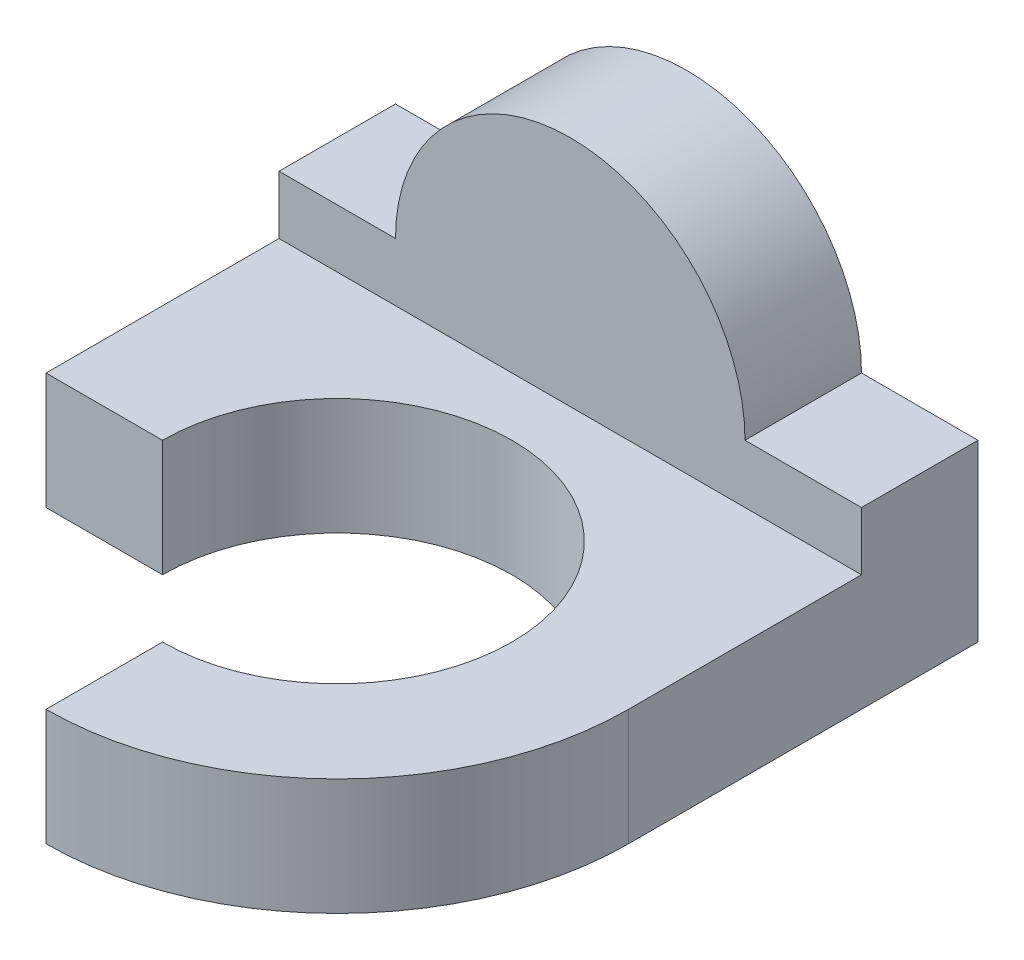
SolidWorks part; units mm, degrees
ref_plane "Front Plane" through (0, 0, 0) normal (0, 0, 1) x (1, 0, 0)
ref_plane "Top Plane" through (0, 0, 0) normal (0, 1, 0) x (1, 0, 0)
ref_plane "Right Plane" through (0, 0, 0) normal (1, 0, 0) x (0, 0, -1)
sketch "Sketch1" plane through (0, 0, 0) normal (0, 0, 1) x (1, 0, 0)
  line L1 (0, 0) -> (100, 0)
  line L2 (0, 0) -> (0, 30)
  line L3 (0, 30) -> (100, 30)
  line L4 (100, 0) -> (100, 30)
  dimension "D1" = 30
  dimension "D2" = 100
extrude "Boss-Extrude1" add sketch "Sketch1" along normal blind 110
sketch "Sketch2" plane through (0, 0, 0) normal (-1, 0, 0) x (0, 0, 1)
  line L1 (110, 30) -> (20, 30)
  line L2 (110, 30) -> (110, 20)
  line L3 (110, 20) -> (20, 20)
  line L4 (20, 30) -> (20, 20)
  dimension "D1" = 10
  dimension "D2" = 20
extrude "Cut-Extrude1" cut sketch "Sketch2" against normal blind 110
sketch "Sketch3" plane through (0, 0, 20) normal (0, 0, 1) x (1, 0, 0)
  line L0 (100, 30) -> (0, 30) construction
  line L1 (20, 30) -> (80, 30)
  arc A0 (20, 30) -> (80, 30) centre (50, 30) cw
  dimension "D1" = 30
extrude "Boss-Extrude2" add sketch "Sketch3" against normal blind 20
sketch "Sketch4" plane through (0, 20, 0) normal (0, 1, 0) x (1, 0, 0)
  line L0 (100, -20) -> (100, -110) construction
  line L3 (50, -110) -> (100, -110)
  line L4 (100, -110) -> (100, -60)
  arc A0 (100, -60) -> (50, -110) centre (50, -60) cw
  dimension "D1" = 50
  dimension "D2" = 40
  dimension "D3" = 50
  dimension "D4" = 50
  dimension "D5" = 50
extrude "Cut-Extrude2" cut sketch "Sketch4" against normal blind 20
sketch "Sketch5" plane through (0, 20, 0) normal (0, 1, 0) x (1, 0, 0)
  line L1 (0, -110) -> (50, -110)
  line L2 (0, -110) -> (0, -60)
  line L3 (0, -60) -> (50, -60)
  line L4 (50, -110) -> (50, -60)
  dimension "D1" = 50
  dimension "D2" = 50
extrude "Cut-Extrude3" cut sketch "Sketch5" against normal blind 20
sketch "Sketch6" plane through (0, 20, 0) normal (0, 1, 0) x (1, 0, 0)
  line L0 (50, -110) -> (50, -60) construction
  line L1 (50, -60) -> (0, -60) construction
  line L2 (20, -60) -> (50, -60)
  line L3 (50, -60) -> (50, -90)
  arc A0 (50, -90) -> (20, -60) centre (50, -60) ccw
  dimension "D1" = 20
extrude "Cut-Extrude4" cut sketch "Sketch6" against normal blind 20
